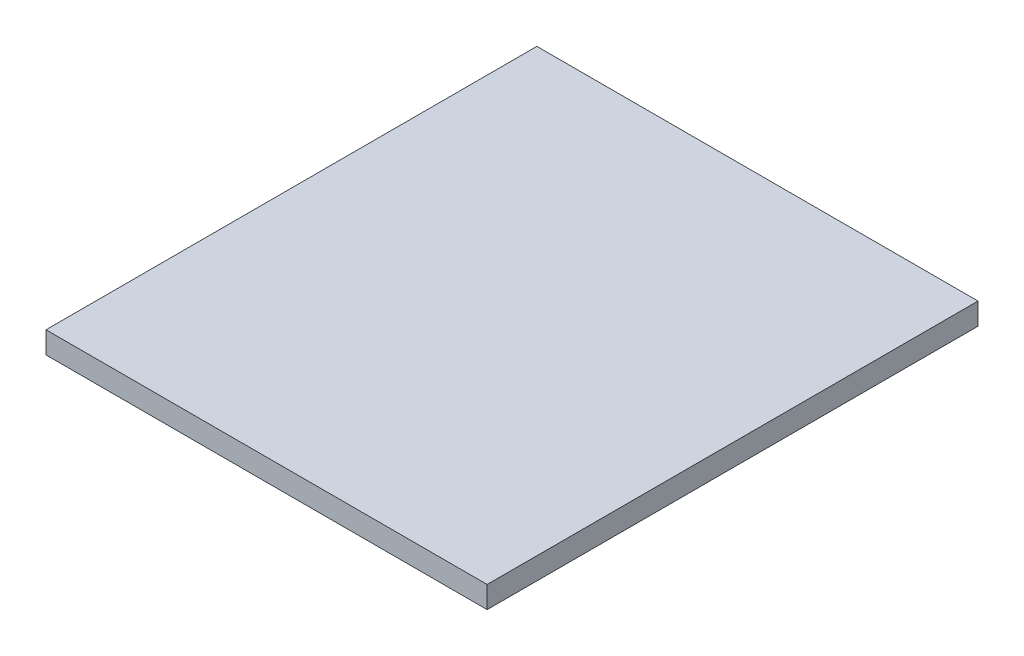
SolidWorks part; units mm, degrees
ref_plane "Front" through (0, 0, 0) normal (0, 0, 1) x (1, 0, 0)
ref_plane "Top" through (0, 0, 0) normal (0, 1, 0) x (1, 0, 0)
ref_plane "Right" through (0, 0, 0) normal (1, 0, 0) x (0, 0, -1)
sketch "Sketch1" plane through (0, 0, 0) normal (0, 1, 0) x (1, 0, 0)
  line L1 (0, 0) -> (20.22, 0)
  line L2 (0, 0) -> (0, 22.5)
  line L3 (0, 22.5) -> (20.22, 22.5)
  line L4 (20.22, 0) -> (20.22, 22.5)
  dimension "D1" = 22.5
  dimension "D2" = 20.22
extrude "Boss-Extrude1" add sketch "Sketch1" along normal blind 1
